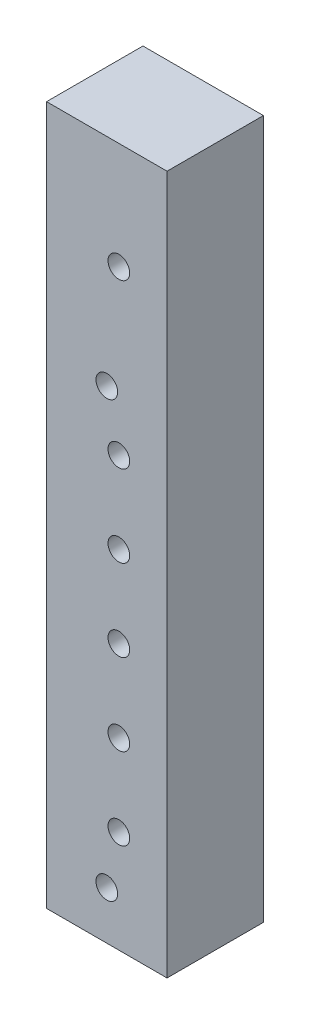
SolidWorks part; units mm, degrees
ref_plane "前基準面" through (0, 0, 0) normal (0, 0, 1) x (1, 0, 0)
ref_plane "上基準面" through (0, 0, 0) normal (0, 1, 0) x (1, 0, 0)
ref_plane "右基準面" through (0, 0, 0) normal (1, 0, 0) x (0, 0, -1)
ref_plane "平面1" through (0, 0, -6) normal (0, 0, -1) x (-1, 0, 0)
sketch "草圖1" plane through (0, 0, -6) normal (0, 0, -1) x (-1, 0, 0)
  line L0 (-7.5, 0) -> (7.5, 0)
  line L1 (7.5, 0) -> (7.5, 87)
  line L2 (7.5, 87) -> (-7.5, 87)
  line L3 (-7.5, 87) -> (-7.5, 0)
  circle A0 centre (-1.5, 22.89) radius 1.35
  circle A1 centre (-1.5, 43.21) radius 1.35
  circle A2 centre (0, 60.1) radius 1.35
  circle A3 centre (0, 6) radius 1.35
  circle A4 centre (-1.5, 12.73) radius 1.35
  circle A5 centre (-1.5, 33.05) radius 1.35
  circle A6 centre (-1.5, 53.37) radius 1.35
  circle A7 centre (-1.5, 73.69) radius 1.35
extrude "填料-伸長1" add sketch "草圖1" against normal blind 12
